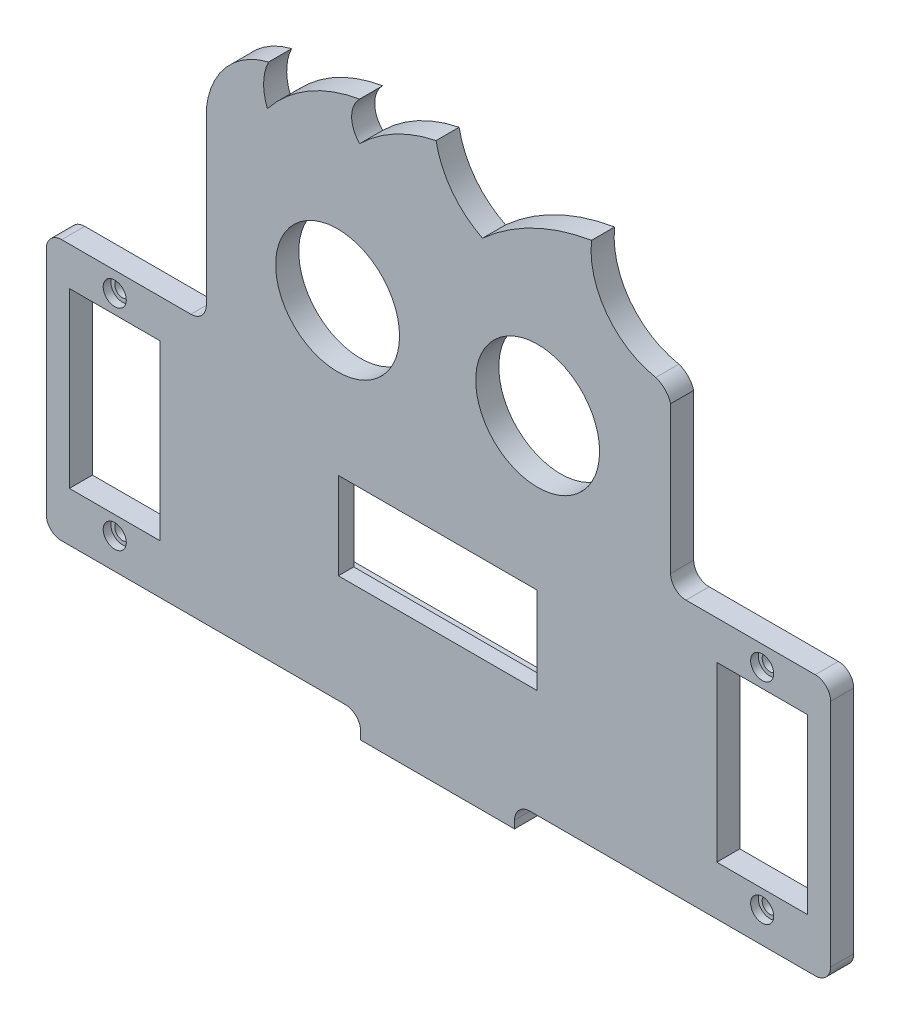
SolidWorks part; units mm, degrees
ref_plane "Alzado" through (0, 0, 0) normal (0, 0, 1) x (1, 0, 0)
ref_plane "Planta" through (0, 0, 0) normal (0, 1, 0) x (1, 0, 0)
ref_plane "Vista lateral" through (0, 0, 0) normal (1, 0, 0) x (0, 0, -1)
sketch "Model" plane through (0, 0, 0) normal (0, 0, 1) x (1, 0, 0)
  line L0 (73.4898, -38.9769) -> (73.4898, -27.6769)
  line L1 (73.4898, -27.6769) -> (47.6898, -27.6769)
  line L2 (47.6898, -27.6769) -> (47.6898, -38.9769)
  line L3 (47.6898, -38.9769) -> (73.4898, -38.9769)
  line L4 (50.5898, -56.0212) -> (70.5898, -56.0212)
  line L5 (47.5898, -8.0208) -> (73.5898, -8.0208) construction
  line L6 (73.5898, -8.0208) -> (60.5898, -8.0208) construction
  line L7 (60.5898, -8.0208) -> (60.5898, -27.6769) construction
  line L8 (60.5898, -27.6769) -> (60.5898, -56.0212) construction
  line L18 (96.8708, -46.621) -> (108.6708, -46.621)
  line L19 (108.6708, -46.621) -> (108.6708, -24.121)
  line L20 (108.6708, -24.121) -> (96.8708, -24.121)
  line L21 (96.8708, -24.121) -> (96.8708, -46.621)
  line L22 (12.7271, -24.121) -> (12.7271, -46.621)
  line L23 (12.7271, -46.621) -> (24.5271, -46.621)
  line L24 (24.5271, -46.621) -> (24.5271, -24.121)
  line L25 (24.5271, -24.121) -> (12.7271, -24.121)
  line L27 (50.5898, -55.021) -> (50.5898, -56.0212)
  line L28 (48.5898, -53.021) -> (32.5271, -53.021)
  line L29 (30.5271, 4.9744) -> (30.5271, -17.121)
  line L30 (90.8708, -17.121) -> (90.8708, 1.979)
  line L31 (88.8708, -53.021) -> (72.5898, -53.021)
  line L32 (70.5898, -56.0212) -> (70.5898, -55.021)
  line L37 (109.6708, -19.121) -> (92.8708, -19.121)
  line L38 (111.6708, -51.021) -> (111.6708, -21.121)
  line L39 (109.6708, -53.021) -> (88.8708, -53.021)
  line L71 (32.5271, -53.021) -> (11.6708, -53.0206)
  line L72 (9.7271, -21.121) -> (9.7271, -51.0769)
  line L73 (28.5271, -19.121) -> (11.7271, -19.121)
  circle A0 centre (47.5898, -8.0208) radius 8.05
  circle A1 centre (73.5898, -8.0208) radius 8.05
  arc A2 (28.5271, -19.121) -> (30.5271, -17.121) centre (28.5271, -17.121) ccw
  arc A3 (92.8708, -19.121) -> (90.8708, -17.121) centre (92.8708, -17.121) cw
  arc A4 (50.5898, -55.021) -> (48.5898, -53.021) centre (48.5898, -55.021) ccw
  arc A5 (72.5898, -53.021) -> (70.5898, -55.021) centre (72.5898, -55.021) ccw
  circle A10 centre (102.7708, -21.721) radius 1
  circle A11 centre (102.7708, -49.021) radius 1
  circle A12 centre (18.6271, -21.721) radius 1
  circle A13 centre (18.6271, -49.021) radius 1
  arc A36 (38.6183, 14.3189) -> (30.5271, 4.9744) centre (41.1247, 3.9735) ccw
  arc A37 (38.6183, 14.3189) -> (38.4712, 8.9961) centre (44.4932, 11.4932) ccw
  arc A38 (50.4388, 16.0514) -> (38.4712, 8.9961) centre (53.6269, -3.0341) ccw
  arc A39 (50.4388, 16.0514) -> (50.4619, 11.0514) centre (52.9503, 13.5629) ccw
  arc A40 (60.3874, 16.3614) -> (50.4619, 11.0514) centre (64.38, -3.0332) ccw
  arc A41 (60.3874, 16.3614) -> (66.4243, 8.3891) centre (71.3781, 18.4121) ccw
  arc A42 (80.5924, 15.2365) -> (66.4243, 8.3891) centre (85.17, -12.3168) ccw
  arc A43 (80.5924, 15.2365) -> (88.9405, 3.9735) centre (90.8379, 14.1051) ccw
  arc A44 (90.8708, 1.979) -> (88.9405, 3.9735) centre (87.9945, 1.1265) ccw
  arc A48 (111.6708, -21.121) -> (109.6708, -19.121) centre (109.6708, -21.121) ccw
  arc A49 (109.6708, -53.021) -> (111.6708, -51.021) centre (109.6708, -51.021) ccw
  arc A66 (9.7271, -51.0769) -> (11.6708, -53.0206) centre (11.6708, -51.0769) ccw
  arc A67 (11.7271, -19.121) -> (9.7271, -21.121) centre (11.7271, -21.121) ccw
  dimension "D1" = 2
  dimension "D2" = 2
  dimension "D4" = 2
  dimension "D3" = 20
extrude "Saliente-Extruir1" add sketch "Model" along normal blind 3
sketch "Croquis2" plane through (0, 0, 0) normal (0, 0, -1) x (-1, 0, 0)
  line L0 (-73.4898, -27.6769) -> (-47.6898, -27.6769) construction
  line L1 (-80.9398, -39.3769) -> (-42.6398, -39.3769)
  line L2 (-80.9398, -39.3769) -> (-80.9398, -27.2769)
  line L3 (-80.9398, -27.2769) -> (-42.6398, -27.2769)
  line L4 (-42.6398, -39.3769) -> (-42.6398, -27.2769)
  line L6 (-47.6898, -27.6769) -> (-47.6898, -38.9769) construction
  dimension "D1" = 38.3
  dimension "D2" = 12.1
  dimension "D3" = 0.4
  dimension "D4" = 5.05
extrude "Cortar-Extruir1" cut sketch "Croquis2" against normal blind 1
sketch "Croquis3" plane through (0, 0, 3) normal (0, 0, 1) x (1, 0, 0)
  circle A0 centre (18.6271, -21.721) radius 1.5
  circle A1 centre (18.6271, -49.021) radius 1.5
  circle A2 centre (102.7708, -49.021) radius 1.5
  circle A3 centre (102.7708, -21.721) radius 1.5
extrude "Cortar-Extruir2" cut sketch "Croquis3" against normal blind 1
sketch "Croquis4" plane through (0, 0, 0) normal (0, 0, -1) x (-1, 0, 0)
  line L1 (-70.5898, -56.0212) -> (-50.5898, -56.0212)
  line L2 (-70.5898, -56.0212) -> (-70.5898, -53.0212)
  line L3 (-70.5898, -53.0212) -> (-50.5898, -53.0212)
  line L4 (-50.5898, -56.0212) -> (-50.5898, -53.0212)
  dimension "D1" = 3
extrude "Saliente-Extruir2" add sketch "Croquis4" along normal blind 8
sketch "Croquis5" plane through (0, -53.0212, 0) normal (0, 1, 0) x (1, 0, 0)
  line L0 (60.5898, 8) -> (60.5898, 0) construction
  line L1 (50.5898, 8) -> (70.5898, 8) construction
  line L2 (50.5898, 0) -> (70.5898, 0) construction
  circle A1 centre (54.5898, 3.5) radius 1.5
  circle A2 centre (66.5898, 3.5) radius 1.5
extrude "Cortar-Extruir3" cut sketch "Croquis5" against normal blind 3
sketch "Croquis6" plane through (0, -53.0212, 0) normal (0, 1, 0) x (1, 0, 0)
  circle A0 centre (66.5898, 3.5) radius 2.25
  circle A1 centre (54.5898, 3.5) radius 2.25
extrude "Cortar-Extruir4" cut sketch "Croquis6" against normal blind 1
fillet "Redondeo1" radius 2 2 edges at (50.5898, -54.5212, -8) (70.5898, -54.5212, -8)
